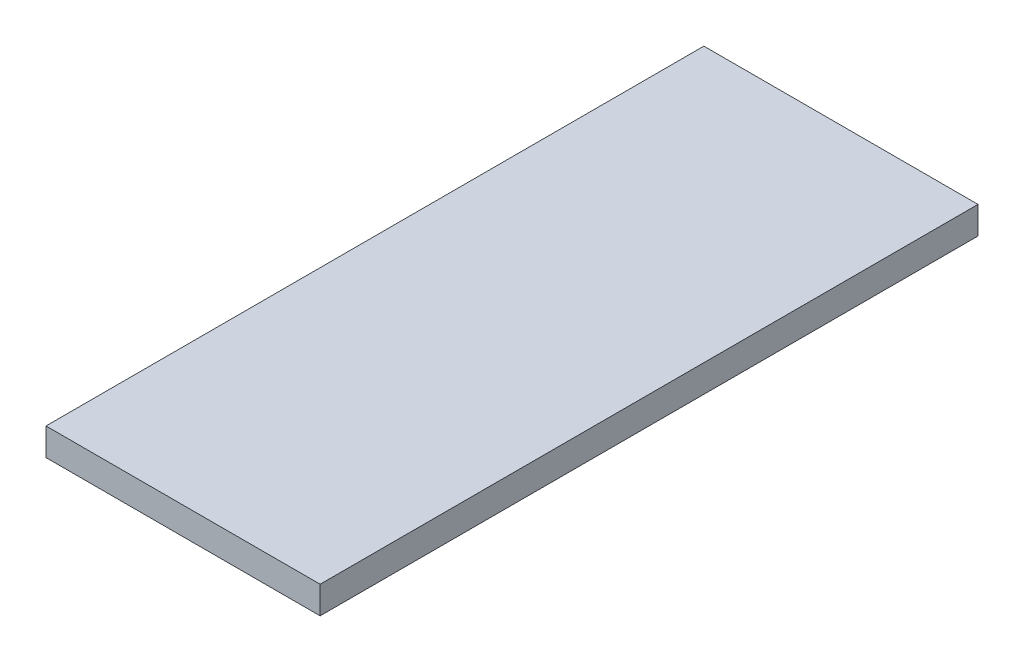
SolidWorks part; units mm, degrees
ref_plane "Спереди" through (0, 0, 0) normal (0, 0, 1) x (1, 0, 0)
ref_plane "Сверху" through (0, 0, 0) normal (0, 1, 0) x (1, 0, 0)
ref_plane "Справа" through (0, 0, 0) normal (1, 0, 0) x (0, 0, -1)
sketch "Эскиз1" plane through (0, 0, 0) normal (0, 1, 0) x (1, 0, 0)
  line L1 (0, 0) -> (50, 0)
  line L2 (0, 0) -> (0, 120)
  line L3 (0, 120) -> (50, 120)
  line L4 (50, 0) -> (50, 120)
extrude "Бобышка-Вытянуть1" add sketch "Эскиз1" along normal blind 5
